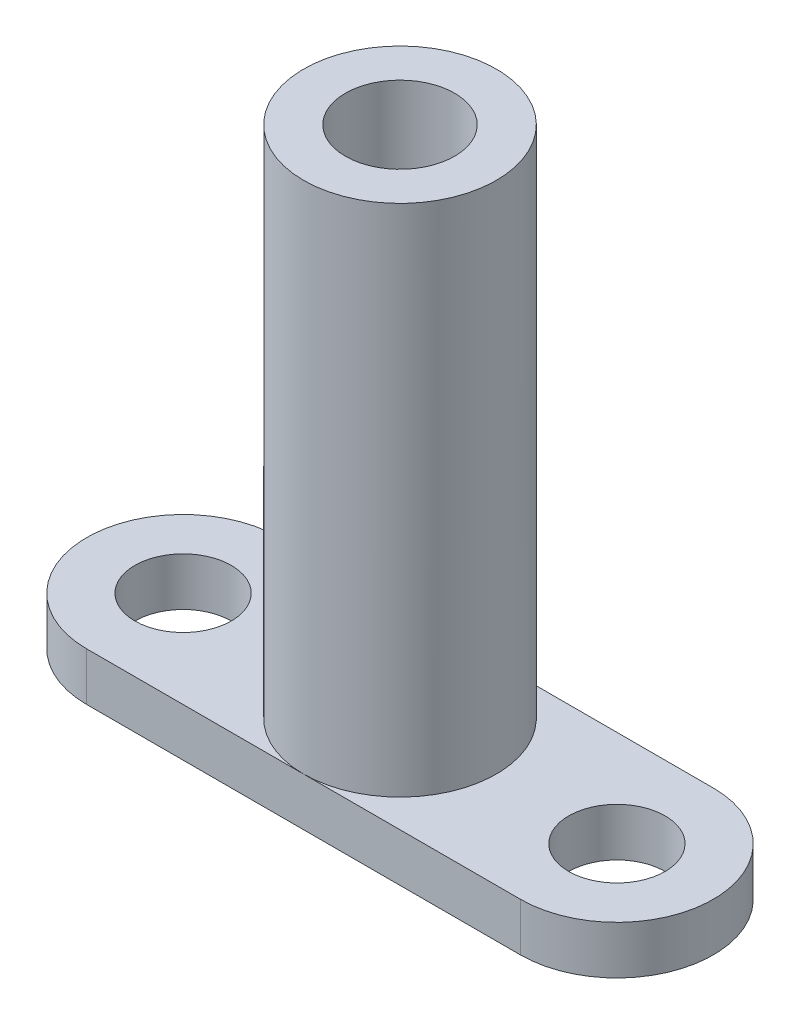
SolidWorks part; units mm, degrees
ref_plane "前视基准面" through (0, 0, 0) normal (0, 0, 1) x (1, 0, 0)
ref_plane "上视基准面" through (0, 0, 0) normal (0, 1, 0) x (1, 0, 0)
ref_plane "右视基准面" through (0, 0, 0) normal (1, 0, 0) x (0, 0, -1)
sketch "草图1" plane through (0, 0, 0) normal (0, 1, 0) x (1, 0, 0)
  line L0 (-13.5, 6) -> (13.5, 6)
  line L1 (-13.5, -6) -> (13.5, -6)
  circle A0 centre (-13.5, 0) radius 6
  circle A1 centre (13.5, 0) radius 6
  dimension "D1" = 12
  dimension "D2" = 13.5
  dimension "D3" = 13.5
extrude "凸台-拉伸1" add sketch "草图1" along normal blind 3 contours A0 | A1 L0 A0 L1 | A1
sketch "草图2" plane through (0, 3, 0) normal (0, 1, 0) x (1, 0, 0)
  circle A0 centre (0, 0) radius 6
extrude "凸台-拉伸2" add sketch "草图2" along normal blind 32
hole_wizard "M8 螺纹孔1" positions "草图3" profile "草图5" tap size "M8" standard "GB" end condition through all
sketch "草图3" plane through (0, 35, 0) normal (0, 1, 0) x (1, 0, 0)
  point P0 (0, 0)
sketch "草图5" plane through (0, 35, 0) normal (1, 0, 0) x (0, 0, 1)
  line L0 (0, 0) -> (0, 35)
  line L1 (0, 35) -> (3.4, 35)
  line L2 (3.4, 35) -> (3.4, 0)
  line L5 (3.4, 0) -> (0, 0)
  line L11 (0, -6.35) -> (0, 107.95) construction
  dimension "通孔螺纹孔钻头直径" = 6.8
  dimension "通孔螺纹孔钻头深度" = 35
cosmetic thread "孔螺蚊线1"
sketch "草图6" plane through (0, 3, 0) normal (0, 1, 0) x (1, 0, 0)
  circle A0 centre (-13.5, 0) radius 3
  circle A1 centre (13.5, 0) radius 3
  dimension "D1" = 6
  dimension "D2" = 6
extrude "切除-拉伸1" cut sketch "草图6" against normal blind 10
